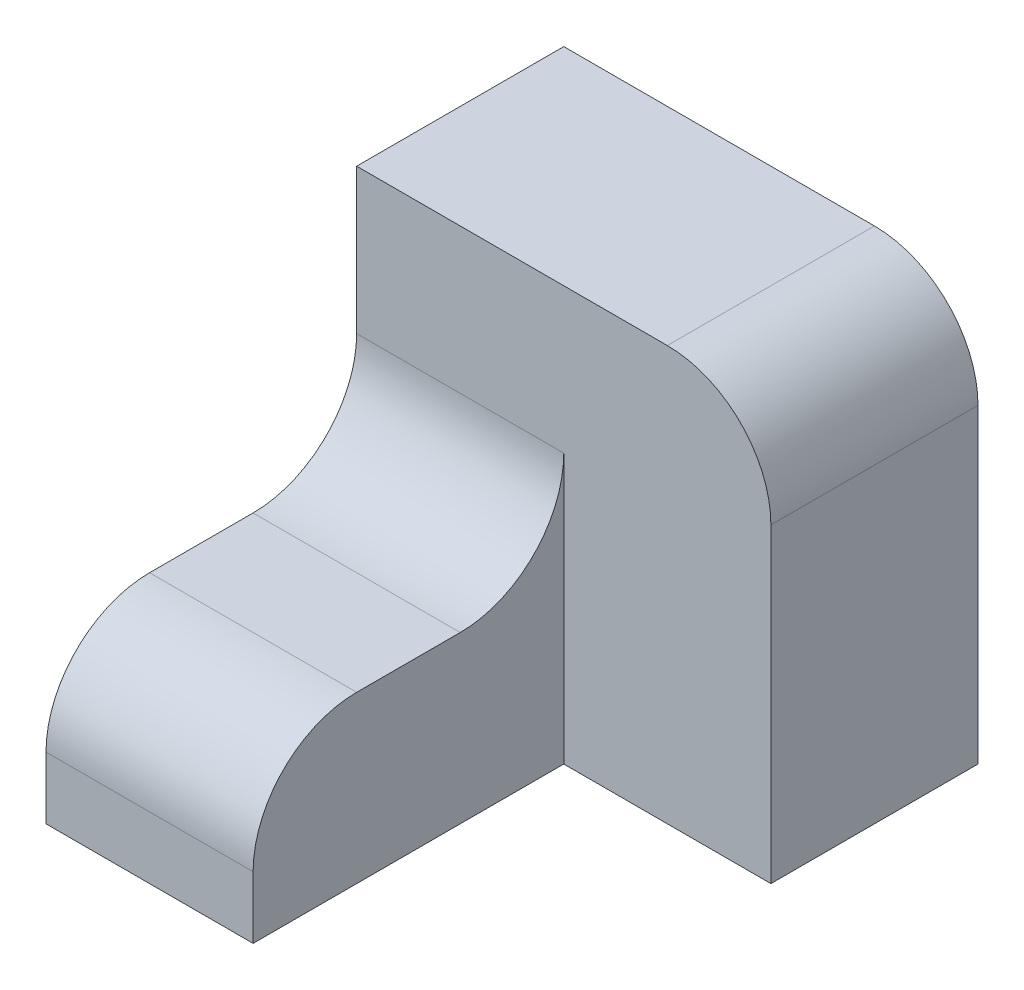
SolidWorks part; units mm, degrees
ref_plane "Front Plane" through (0, 0, 0) normal (0, 0, 1) x (1, 0, 0)
ref_plane "Top Plane" through (0, 0, 0) normal (0, 1, 0) x (1, 0, 0)
ref_plane "Right Plane" through (0, 0, 0) normal (1, 0, 0) x (0, 0, -1)
sketch "Sketch1" plane through (0, 0, 0) normal (0, 0, 1) x (1, 0, 0)
  line L1 (-30, -16) -> (-10, -16)
  line L2 (-10, -16) -> (-10, 0)
  line L3 (-10, 0) -> (-30, 0)
  line L4 (-30, 0) -> (-30, -16)
  dimension "D1" = 20
  dimension "Width" = 16
extrude "Boss-Extrude1" add sketch "Sketch1" along normal blind 30
sketch "Sketch2" plane through (0, 0, 0) normal (0, 0, 1) x (1, 0, 0)
  line L1 (-30, -16) -> (10, -16)
  line L2 (10, -16) -> (10, 24)
  line L3 (10, 24) -> (-30, 24)
  line L4 (-30, 24) -> (-30, -16)
  dimension "D1" = 40
  dimension "Width" = 40
extrude "Boss-Extrude2" add sketch "Sketch2" against normal blind 20
fillet "Fillet1" radius 10 3 edges at (-20, 0, 0) (10, 24, -10) (-20, 0, 30)
